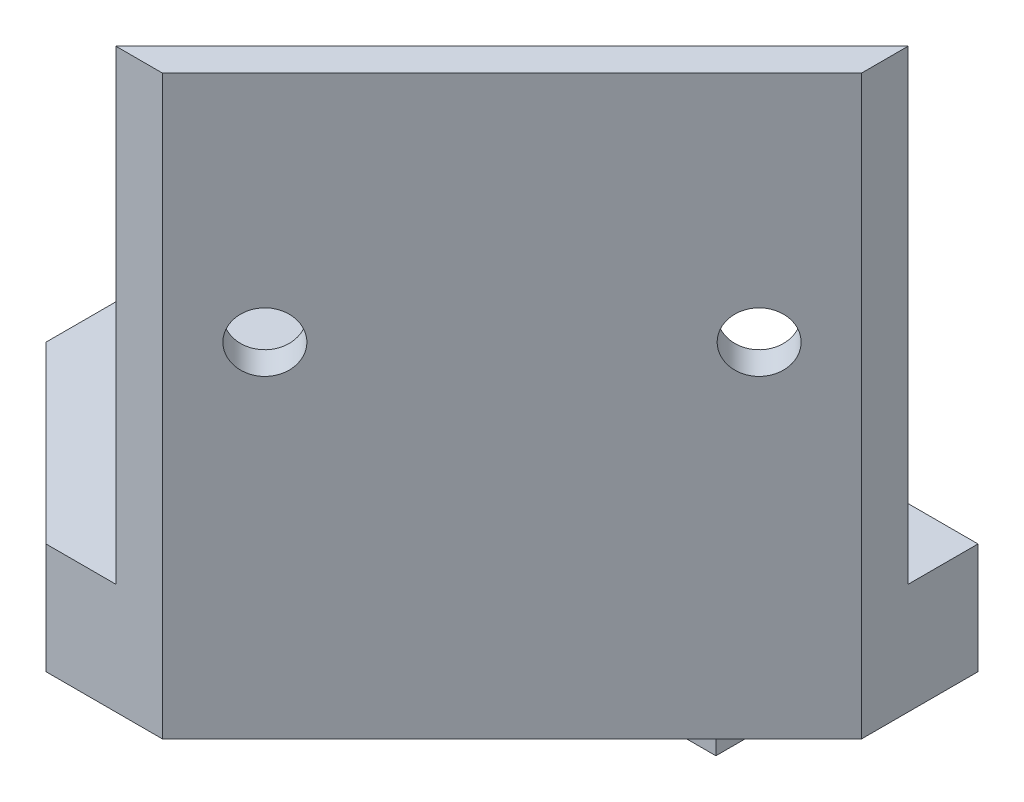
SolidWorks part; units mm, degrees
ref_plane "Front Plane" through (0, 0, 0) normal (0, 0, 1) x (1, 0, 0)
ref_plane "Top Plane" through (0, 0, 0) normal (0, 1, 0) x (1, 0, 0)
ref_plane "Right Plane" through (0, 0, 0) normal (1, 0, 0) x (0, 0, -1)
sketch "Sketch1" plane through (0, 0, 0) normal (0, 0, 1) x (1, 0, 0)
  line L1 (0, 0) -> (40, 0)
  line L2 (0, 0) -> (0, -10)
  line L3 (0, -10) -> (40, -10)
  line L4 (40, 0) -> (40, -10)
  dimension "D1" = 40
  dimension "D2" = 10
extrude "Boss-Extrude1" add sketch "Sketch1" along normal blind 7.5
sketch "Sketch2" plane through (0, 0, 7.5) normal (0, 0, 1) x (1, 0, 0)
  line L0 (20, 0) -> (20, -10) construction
  line L1 (40, 0) -> (0, 0) construction
  line L2 (0, -10) -> (40, -10) construction
  line L3 (0, -5) -> (20, -5) construction
  line L4 (0, 0) -> (0, -10) construction
  point P10 (5, -5)
  point P11 (35, -5)
  dimension "D1" = 30
hole_wizard "CBORE for M3 SHCS1" positions "Sketch2" profile "Sketch3" counterbore size "M3" standard "ANSI Metric" end condition through all
sketch "Sketch3" plane through (35, -5, 7.5) normal (1, 0, 0) x (0, -1, 0)
  line L0 (0, 0) -> (0, 7.5)
  line L1 (0, 7.5) -> (1.7, 7.5)
  line L3 (1.7, 7.5) -> (1.7, 3)
  line L4 (3.25, 3) -> (1.7, 3)
  line L5 (3.25, 3) -> (3.25, 0.025)
  line L6 (3.25, 0.025) -> (3.275, 0)
  line L7 (3.275, 0) -> (0, 0)
  line L8 (-3.25, 0.025) -> (-3.275, 0) construction
  line L11 (0, -6.35) -> (0, 107.95) construction
  dimension "Thru Hole Dia." = 3.4
  dimension "Thru Hole Depth" = 7.5
  dimension "C'Bore Dia." = 6.5
  dimension "C'Bore Depth" = 3
  dimension "Near C'Sink Dia." = 6.55
  dimension "Near C'Sink Angle" = 90
sketch "Sketch4" plane through (0, 0, 0) normal (0, 0, 1) x (1, 0, 0)
  line L0 (0, 0) -> (0, -10) construction
  line L12 (0, 9.5) -> (55, 9.5)
  line L13 (0, 9.5) -> (0, 0)
  line L14 (0, 0) -> (55, 0)
  line L15 (55, 9.5) -> (55, 0)
  line L16 (40, 0) -> (0, 0) construction
  dimension "D1" = 55
  dimension "D2" = 9.5
extrude "Boss-Extrude2" add sketch "Sketch4" along normal blind 40
sketch "Sketch5" plane through (0, 9.5, 0) normal (0, 1, 0) x (1, 0, 0)
  line L1 (55, -10) -> (25, -40)
  line L2 (55, -40) -> (55, 0) construction
  line L12 (55, -40) -> (0, -40) construction
  line L13 (55, -6) -> (21, -40)
  line L14 (21, -40) -> (25, -40)
  line L15 (55, -6) -> (55, -10)
  dimension "D1" = 30
  dimension "D2" = 30
  dimension "D3" = 4
extrude "Boss-Extrude3" add sketch "Sketch5" along normal blind 40
sketch "Sketch7" plane through (0, 9.5, 0) normal (0, 1, 0) x (1, 0, 0)
  line L4 (55, -10) -> (25, -40)
  line L9 (25, -40) -> (55, -40)
  line L10 (55, -40) -> (55, -10)
  line L15 (55, -10) -> (25, -40)
  line L16 (25, -40) -> (55, -40)
  line L17 (55, -40) -> (55, -10)
  dimension "D1" = 0
extrude "Cut-Extrude1" cut sketch "Sketch7" against normal through all
sketch "Sketch8" plane through (30.5, 0, 30.5) normal (-0.7071, 0, -0.7071) x (-0.7071, 0, 0.7071)
  line L0 (-25.6066, 29.5) -> (4.3934, 29.5) construction
  line L1 (-10.6066, 49.5) -> (-10.6066, 41.624) construction
  line L2 (-34.6482, 49.5) -> (13.435, 49.5) construction
  point P6 (-10.6066, 29.5)
  point P9 (-25.6066, 29.5)
  point P12 (4.3934, 29.5)
  dimension "D1" = 30
  dimension "D2" = 20
hole_wizard "Ø5.1 (5.1) Diameter Hole1" positions "Sketch8" profile "Sketch10" hole size "Ø5.1" standard "ANSI Metric" end condition up to next
sketch "Sketch10" plane through (27.3934, 29.5, 33.6066) normal (0, 1, 0) x (-0.7071, 0, 0.7071)
  line L0 (0, 0) -> (0, 2.8284)
  line L1 (0, 2.8284) -> (2.55, 2.8284)
  line L2 (2.55, 2.8284) -> (2.55, 0.025)
  line L3 (2.55, 0.025) -> (2.575, 0)
  line L5 (2.575, 0) -> (0, 0)
  line L6 (-2.55, 0.025) -> (-2.575, 0) construction
  line L11 (0, -6.35) -> (0, 107.95) construction
  dimension "Thru Hole Dia." = 5.1
  dimension "Thru Hole Depth" = 2.8284
  dimension "Near C'Sink Dia." = 5.15
  dimension "Near C'Sink Angle" = 90
sketch "Sketch11" plane through (0, 9.5, 0) normal (0, 1, 0) x (1, 0, 0)
  line L5 (0, -25) -> (0, -40)
  line L6 (0, -40) -> (0, 0) construction
  line L7 (0, -40) -> (15, -40)
  line L8 (21, -40) -> (0, -40) construction
  line L9 (15, -40) -> (0, -25)
  dimension "D1" = 15
extrude "Cut-Extrude2" cut sketch "Sketch11" against normal through all
equation "\"D2@Sketch5\"=\"D1@Sketch5\""
